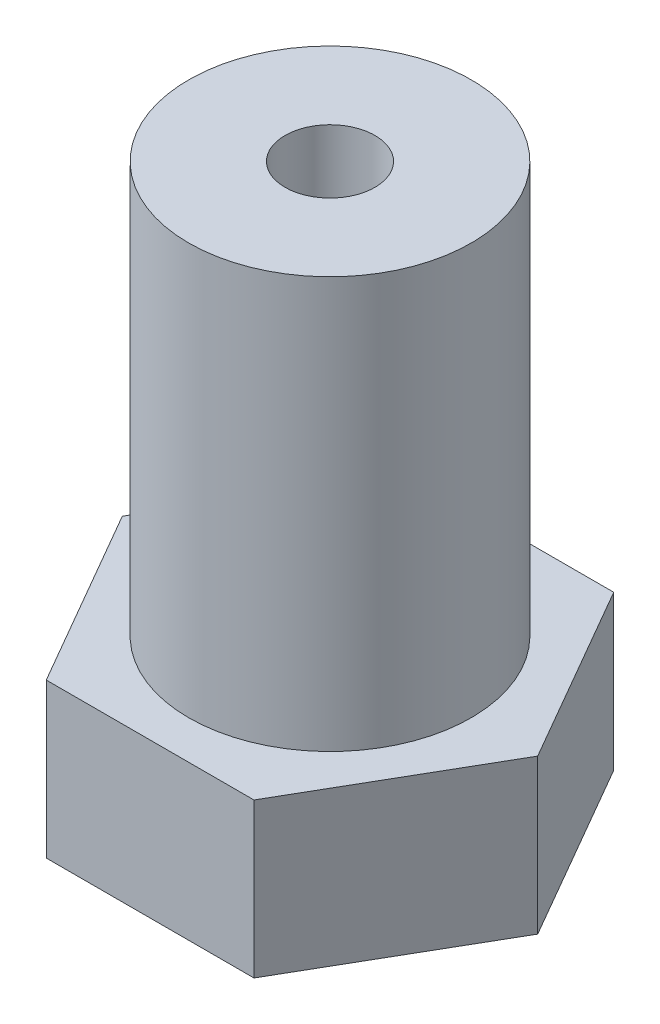
SolidWorks part; units mm, degrees
ref_plane "Front Plane" through (0, 0, 0) normal (0, 0, 1) x (1, 0, 0)
ref_plane "Top Plane" through (0, 0, 0) normal (0, 1, 0) x (1, 0, 0)
ref_plane "Right Plane" through (0, 0, 0) normal (1, 0, 0) x (0, 0, -1)
sketch "Sketch1" plane through (0, 0, 0) normal (0, 1, 0) x (1, 0, 0)
  line L1 (8.0829, 0) -> (4.0415, 7)
  line L2 (4.0415, 7) -> (-4.0415, 7)
  line L3 (-4.0415, 7) -> (-8.0829, 0)
  line L4 (-8.0829, 0) -> (-4.0415, -7)
  line L5 (-4.0415, -7) -> (4.0415, -7)
  line L6 (4.0415, -7) -> (8.0829, 0)
  circle A0 centre (0, 0) radius 7 construction
  dimension "D1" = 14
extrude "Boss-Extrude1" add sketch "Sketch1" along normal blind 6
sketch "Sketch2" plane through (0, 6, 0) normal (0, 1, 0) x (1, 0, 0)
  circle A0 centre (0, 0) radius 5.5
  circle A1 centre (0, 0) radius 1.75
  dimension "D1" = 11
  dimension "D2" = 3.5
extrude "Boss-Extrude2" add sketch "Sketch2" along normal blind 16
